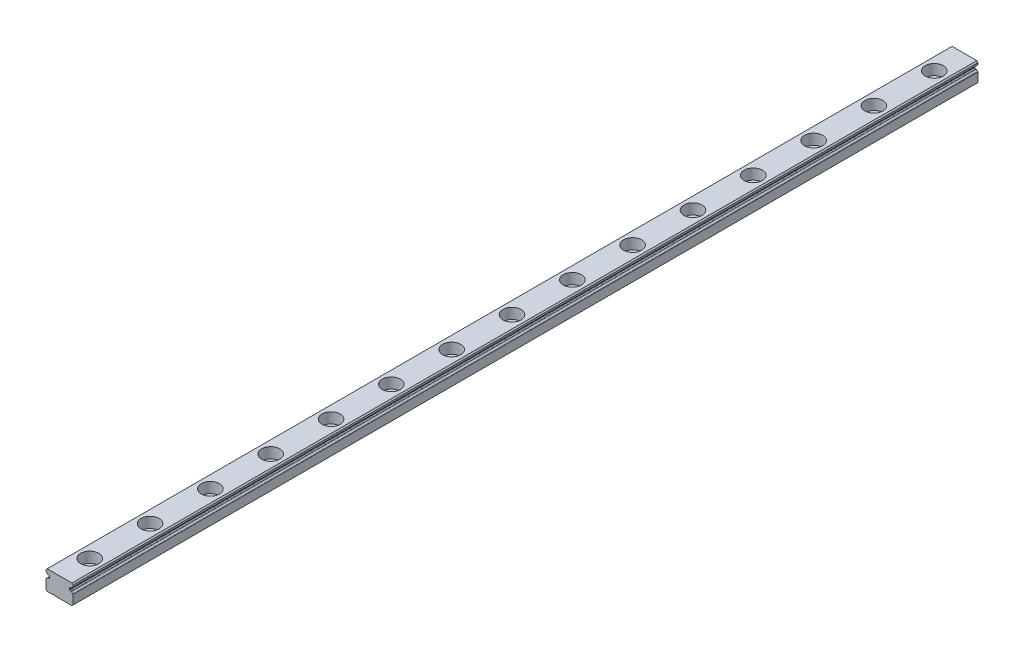
SolidWorks part; units mm, degrees
ref_plane "Front Plane" through (0, 0, 0) normal (0, 0, 1) x (1, 0, 0)
ref_plane "Top Plane" through (0, 0, 0) normal (0, 1, 0) x (1, 0, 0)
ref_plane "Right Plane" through (0, 0, 0) normal (1, 0, 0) x (0, 0, -1)
ref_plane "Plane1" through (0, 0, 300) normal (0, 0, 1) x (1, 0, 0)
sketch "Sketch1" plane through (0, 0, 300) normal (0, 0, 1) x (1, 0, 0)
  line L0 (-4.5, -0.4) -> (-4.5, -6.5)
  line L1 (-4.5, -6.5) -> (4.5, -6.5)
  line L2 (4.5, -6.5) -> (4.5, -0.4)
  line L3 (4.5, -0.4) -> (4.1, 0)
  line L4 (4.1, 0) -> (-4.1, 0)
  line L5 (-4.1, 0) -> (-4.5, -0.4)
extrude "Boss-Extrude1" add sketch "Sketch1" against normal blind 600
sketch "Sketch2" plane through (0, 0, -300) normal (0, 0, -1) x (-1, 0, 0)
  line L0 (4.5, -2.9539) -> (4.5, -1.5044)
  line L1 (4.5, -1.5044) -> (3.3, -1.6093)
  line L2 (3.3, -1.6093) -> (3.3, -2.3907)
  line L3 (3.3, -2.3907) -> (3.9037, -2.4435)
  arc A0 (3.9037, -2.4435) -> (4.5, -2.9539) centre (4.8, -2) ccw
extrude "Cut-Extrude1" cut sketch "Sketch2" against normal through all
sketch "Sketch3" plane through (0, 0, -300) normal (0, 0, -1) x (-1, 0, 0)
  line L0 (1.4, -6.5) -> (2.2, -6.5)
  arc A0 (2.2, -6.5) -> (1.4, -6.5) centre (1.8, -6.8) ccw
extrude "Cut-Extrude2" cut sketch "Sketch3" against normal blind 600
sketch "Sketch4" plane through (0, 0, -300) normal (0, 0, -1) x (-1, 0, 0)
  line L0 (-4.5, -1.5044) -> (-4.5, -2.9539)
  line L1 (-3.9037, -2.4435) -> (-3.3, -2.3907)
  line L2 (-3.3, -2.3907) -> (-3.3, -1.6093)
  line L3 (-3.3, -1.6093) -> (-4.5, -1.5044)
  arc A0 (-4.5, -2.9539) -> (-3.9037, -2.4435) centre (-4.8, -2) ccw
extrude "Cut-Extrude3" cut sketch "Sketch4" against normal through all
sketch "Sketch5" plane through (0, 0, -300) normal (0, 0, -1) x (-1, 0, 0)
  line L0 (-4.5, -1.0461) -> (-4.5, -1.5044)
  line L1 (-4.5, -1.5044) -> (-3.9037, -1.5565)
  arc A0 (-3.9037, -1.5565) -> (-4.5, -1.0461) centre (-4.8, -2) ccw
extrude "Cut-Extrude4" cut sketch "Sketch5" against normal through all
sketch "Sketch6" plane through (0, 0, -300) normal (0, 0, -1) x (-1, 0, 0)
  line L0 (3.9037, -1.5565) -> (4.5, -1.5044)
  line L1 (4.5, -1.5044) -> (4.5, -1.0461)
  arc A0 (4.5, -1.0461) -> (3.9037, -1.5565) centre (4.8, -2) ccw
extrude "Cut-Extrude5" cut sketch "Sketch6" against normal through all
hole_wizard "CBORE for M3 Hex Head Machine Screw1" positions "Sketch8" profile "Sketch7" counterbore size "M3" standard "ANSI Metric"
sketch "Sketch8" plane through (0, 0, 0) normal (0, 1, 0) x (1, 0, 0)
  point P0 (0, -287.5)
  point P1 (0, -267.5)
  point P2 (0, -247.5)
  point P3 (0, -227.5)
  point P4 (0, -207.5)
  point P5 (0, -187.5)
  point P6 (0, -167.5)
  point P7 (0, -147.5)
  point P8 (0, -127.5)
  point P9 (0, -107.5)
  point P10 (0, -87.5)
  point P11 (0, -67.5)
  point P12 (0, -47.5)
  point P13 (0, -27.5)
  point P14 (0, -7.5)
  point P15 (0, 12.5)
  point P16 (0, 32.5)
  point P17 (0, 52.5)
  point P18 (0, 72.5)
  point P19 (0, 92.5)
  point P20 (0, 112.5)
  point P21 (0, 132.5)
  point P22 (0, 152.5)
  point P23 (0, 172.5)
  point P24 (0, 192.5)
  point P25 (0, 212.5)
  point P26 (0, 232.5)
  point P27 (0, 252.5)
  point P28 (0, 272.5)
  point P29 (0, 292.5)
sketch "Sketch7" plane through (0, 0, 287.5) normal (1, 0, 0) x (0, 0, 1)
  line L0 (0, 0) -> (0, 6.5)
  line L1 (0, 6.5) -> (1.75, 6.5)
  line L3 (1.75, 6.5) -> (1.75, 3.5)
  line L4 (1.75, 3.5) -> (3, 3.5)
  line L5 (3, 3.5) -> (3, 0)
  line L7 (3, 0) -> (0, 0)
  line L11 (0, -6.35) -> (0, 107.95) construction
  dimension "Thru Hole Dia." = 3.5
  dimension "Thru Hole Depth" = 6.5
  dimension "C'Bore Dia." = 6
  dimension "C'Bore Depth" = 3.5
chamfer "Chamfer1" distance 0.4 angle 45 2 edges at (4.5, -6.5, 0) (-4.5, -6.5, 0)
fillet "Fillet1" radius 0.15 12 edges at (-3.9037, -1.5565, 0) (-4.5, -1.0461, 0) (-4.5, -2.9539, 0) (3.3, -1.6093, 0) (3.9037, -2.4435, 0) (4.5, -2.9539, 0) (-3.3, -2.3907, 0) (4.5, -1.0461, 0) (3.3, -2.3907, 0) (-3.3, -1.6093, 0) (-3.9037, -2.4435, 0) (3.9037, -1.5565, 0)
sketch "Sketch9" plane through (0, 0, 300) normal (0, 0, 1) x (1, 0, 0)
  line L1 (7.0362, -8.0336) -> (-8.0556, -8.0336)
  line L2 (7.0362, -8.0336) -> (7.0362, 2.0736)
  line L3 (7.0362, 2.0736) -> (-8.0556, 2.0736)
  line L4 (-8.0556, -8.0336) -> (-8.0556, 2.0736)
  line L5 (7.0362, -8.0336) -> (-8.0556, 2.0736) construction
  line L6 (7.0362, 2.0736) -> (-8.0556, -8.0336) construction
  point P0 (-0.5097, -2.98)
extrude "Cut-Extrude6" cut sketch "Sketch9" against normal blind 302.5
sketch "Sketch10" plane through (0, 0, -300) normal (0, 0, -1) x (-1, 0, 0)
  line L17 (3.4369, -1.5974) -> (3.8235, -1.5635)
  line L18 (4.5, -0.9417) -> (4.5, -0.4)
  line L19 (4.5, -0.4) -> (4.1, 0)
  line L20 (4.1, 0) -> (-4.1, 0)
  line L21 (-4.1, 0) -> (-4.5, -0.4)
  line L22 (-4.5, -0.4) -> (-4.5, -0.9417)
  line L23 (-3.8235, -1.5635) -> (-3.4369, -1.5974)
  line L24 (-3.3, -1.7468) -> (-3.3, -2.2532)
  line L25 (-3.4369, -2.4026) -> (-3.8235, -2.4365)
  line L26 (-4.5, -3.0583) -> (-4.5, -6.1)
  line L27 (-4.5, -6.1) -> (-4.1, -6.5)
  line L28 (-4.1, -6.5) -> (1.4, -6.5)
  line L29 (2.2, -6.5) -> (4.1, -6.5)
  line L30 (4.1, -6.5) -> (4.5, -6.1)
  line L31 (4.5, -6.1) -> (4.5, -3.0583)
  line L32 (3.8235, -2.4365) -> (3.4369, -2.4026)
  line L33 (3.3, -2.2532) -> (3.3, -1.7468)
  line L34 (3.4369, -1.5974) -> (3.8235, -1.5635)
  line L35 (4.5, -0.9417) -> (4.5, -0.4)
  line L36 (4.5, -0.4) -> (4.1, 0)
  line L37 (4.1, 0) -> (-4.1, 0)
  line L38 (-4.1, 0) -> (-4.5, -0.4)
  line L39 (-4.5, -0.4) -> (-4.5, -0.9417)
  line L40 (-3.8235, -1.5635) -> (-3.4369, -1.5974)
  line L41 (-3.3, -1.7468) -> (-3.3, -2.2532)
  line L42 (-3.4369, -2.4026) -> (-3.8235, -2.4365)
  line L43 (-4.5, -3.0583) -> (-4.5, -6.1)
  line L44 (-4.5, -6.1) -> (-4.1, -6.5)
  line L45 (-4.1, -6.5) -> (1.4, -6.5)
  line L46 (2.2, -6.5) -> (4.1, -6.5)
  line L47 (4.1, -6.5) -> (4.5, -6.1)
  line L48 (4.5, -6.1) -> (4.5, -3.0583)
  line L49 (3.8235, -2.4365) -> (3.4369, -2.4026)
  line L50 (3.3, -2.2532) -> (3.3, -1.7468)
  arc A17 (3.8235, -1.5635) -> (3.9395, -1.4905) centre (3.8104, -1.4141) ccw
  arc A18 (4.4087, -1.0797) -> (3.9395, -1.4905) centre (4.8, -2) ccw
  arc A19 (4.4087, -1.0797) -> (4.5, -0.9417) centre (4.35, -0.9417) ccw
  arc A20 (-4.5, -0.9417) -> (-4.4087, -1.0797) centre (-4.35, -0.9417) ccw
  arc A21 (-3.9395, -1.4905) -> (-4.4087, -1.0797) centre (-4.8, -2) ccw
  arc A22 (-3.9395, -1.4905) -> (-3.8235, -1.5635) centre (-3.8104, -1.4141) ccw
  arc A23 (-3.3, -1.7468) -> (-3.4369, -1.5974) centre (-3.45, -1.7468) ccw
  arc A24 (-3.4369, -2.4026) -> (-3.3, -2.2532) centre (-3.45, -2.2532) ccw
  arc A25 (-3.8235, -2.4365) -> (-3.9395, -2.5095) centre (-3.8104, -2.5859) ccw
  arc A26 (-4.4087, -2.9203) -> (-3.9395, -2.5095) centre (-4.8, -2) ccw
  arc A27 (-4.4087, -2.9203) -> (-4.5, -3.0583) centre (-4.35, -3.0583) ccw
  arc A28 (2.2, -6.5) -> (1.4, -6.5) centre (1.8, -6.8) ccw
  arc A29 (4.5, -3.0583) -> (4.4087, -2.9203) centre (4.35, -3.0583) ccw
  arc A30 (3.9395, -2.5095) -> (4.4087, -2.9203) centre (4.8, -2) ccw
  arc A31 (3.9395, -2.5095) -> (3.8235, -2.4365) centre (3.8104, -2.5859) ccw
  arc A32 (3.3, -2.2532) -> (3.4369, -2.4026) centre (3.45, -2.2532) ccw
  arc A33 (3.4369, -1.5974) -> (3.3, -1.7468) centre (3.45, -1.7468) ccw
  arc A34 (3.8235, -1.5635) -> (3.9395, -1.4905) centre (3.8104, -1.4141) ccw
  arc A35 (4.4087, -1.0797) -> (3.9395, -1.4905) centre (4.8, -2) ccw
  arc A36 (4.4087, -1.0797) -> (4.5, -0.9417) centre (4.35, -0.9417) ccw
  arc A37 (-4.5, -0.9417) -> (-4.4087, -1.0797) centre (-4.35, -0.9417) ccw
  arc A38 (-3.9395, -1.4905) -> (-4.4087, -1.0797) centre (-4.8, -2) ccw
  arc A39 (-3.9395, -1.4905) -> (-3.8235, -1.5635) centre (-3.8104, -1.4141) ccw
  arc A40 (-3.3, -1.7468) -> (-3.4369, -1.5974) centre (-3.45, -1.7468) ccw
  arc A41 (-3.4369, -2.4026) -> (-3.3, -2.2532) centre (-3.45, -2.2532) ccw
  arc A42 (-3.8235, -2.4365) -> (-3.9395, -2.5095) centre (-3.8104, -2.5859) ccw
  arc A43 (-4.4087, -2.9203) -> (-3.9395, -2.5095) centre (-4.8, -2) ccw
  arc A44 (-4.4087, -2.9203) -> (-4.5, -3.0583) centre (-4.35, -3.0583) ccw
  arc A45 (2.2, -6.5) -> (1.4, -6.5) centre (1.8, -6.8) ccw
  arc A46 (4.5, -3.0583) -> (4.4087, -2.9203) centre (4.35, -3.0583) ccw
  arc A47 (3.9395, -2.5095) -> (4.4087, -2.9203) centre (4.8, -2) ccw
  arc A48 (3.9395, -2.5095) -> (3.8235, -2.4365) centre (3.8104, -2.5859) ccw
  arc A49 (3.3, -2.2532) -> (3.4369, -2.4026) centre (3.45, -2.2532) ccw
  arc A50 (3.4369, -1.5974) -> (3.3, -1.7468) centre (3.45, -1.7468) ccw
  dimension "D1" = 0
extrude "Boss-Extrude2" add sketch "Sketch10" along normal blind 2.5
